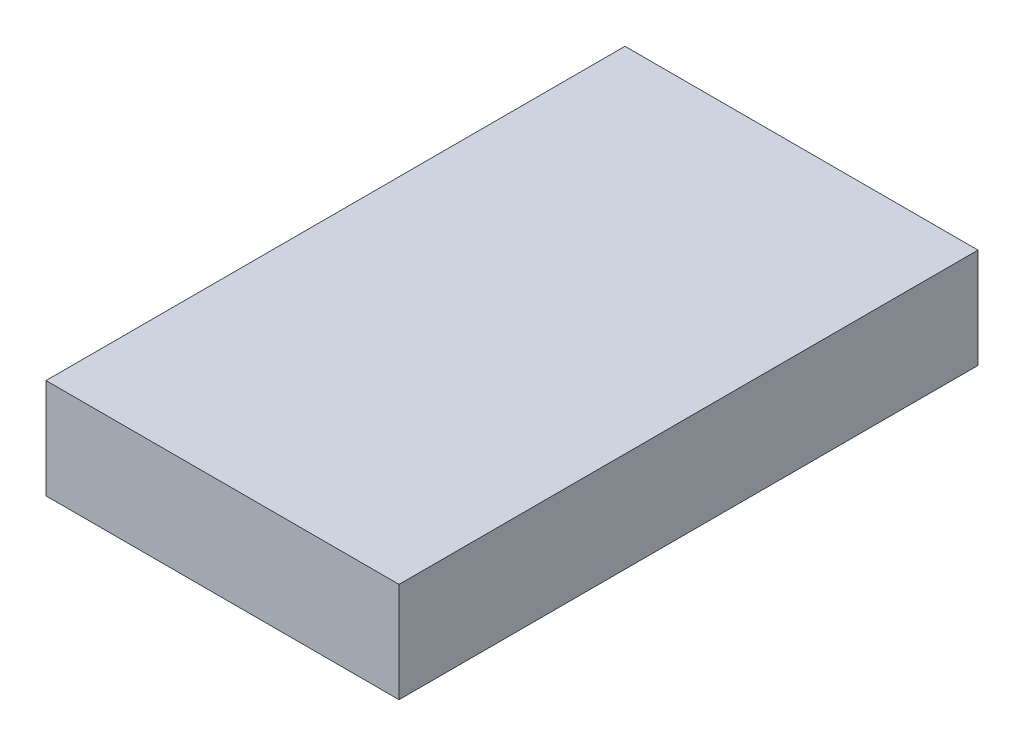
SolidWorks part; units mm, degrees
ref_plane "Front Plane" through (0, 0, 0) normal (0, 0, 1) x (1, 0, 0)
ref_plane "Top Plane" through (0, 0, 0) normal (0, 1, 0) x (1, 0, 0)
ref_plane "Right Plane" through (0, 0, 0) normal (1, 0, 0) x (0, 0, -1)
sketch "Sketch1" plane through (0, 0, 0) normal (0, 1, 0) x (1, 0, 0)
  line L1 (0, 0) -> (50, 0)
  line L2 (0, 0) -> (0, -82)
  line L3 (0, -82) -> (50, -82)
  line L4 (50, 0) -> (50, -82)
  dimension "D1" = 50
  dimension "D2" = 82
extrude "Boss-Extrude1" add sketch "Sketch1" along normal blind 14.15
